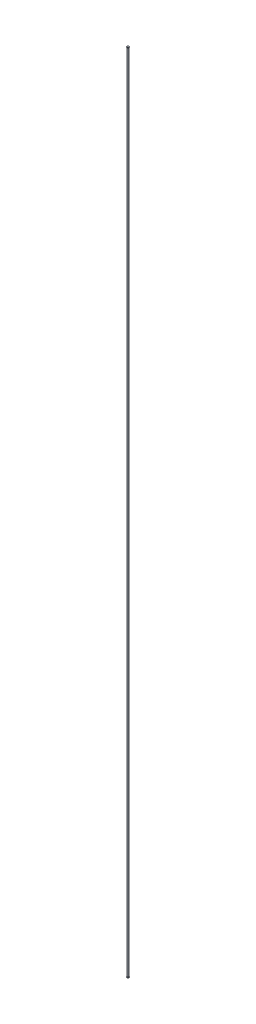
SolidWorks part; units mm, degrees
material "6061-T6 (SS)"
ref_plane "Front Plane" through (0, 0, 0) normal (0, 0, 1) x (1, 0, 0)
ref_plane "Top Plane" through (0, 0, 0) normal (0, 1, 0) x (1, 0, 0)
ref_plane "Right Plane" through (0, 0, 0) normal (1, 0, 0) x (0, 0, -1)
sketch "Sketch1" plane through (0, 0, 0) normal (0, 1, 0) x (1, 0, 0)
  circle A0 centre (0, 0) radius 3.175
  circle A1 centre (0, 0) radius 6.35
  dimension "D1" = 12.7
  dimension "D2" = 6.35
extrude "Boss-Extrude1" add sketch "Sketch1" along normal blind 7781.036
sketch "Sketch2" plane through (0, 0, 0) normal (1, 0, 0) x (0, 0, -1)
  line L0 (6.35, 7781.036) -> (10.4317, 7785.9004)
  line L1 (6.35, 7781.036) -> (-6.35, 7781.036) construction
  line L2 (3.175, 7781.036) -> (8.5685, 7787.4638)
  line L3 (3.175, 7781.036) -> (-3.175, 7781.036) construction
  line L4 (6.35, 7781.036) -> (9.8632, 7781.036) construction
  line L5 (10.4317, 7785.9004) -> (8.5685, 7787.4638)
  line L6 (6.35, 7781.036) -> (3.175, 7781.036)
  dimension "D1" = 50
  dimension "D2" = 6.35
  dimension "D3" = 8.3909
  dimension "D4" = 3.175
ref_axis "Axis1" through (0, 8176.5703, 0) along (0, -1, 0)
revolve "Revolve1" add sketch "Sketch2" angle 360 about axis through (0, 8176.5703, 0) along (0, -1, 0)
ref_plane "Plane1" through (0, 3890.518, 0) normal (0, 1, 0) x (1, 0, 0)
mirror "Mirror1" about plane through (0, 3890.518, 0) normal (0, 1, 0) of "Revolve1"
